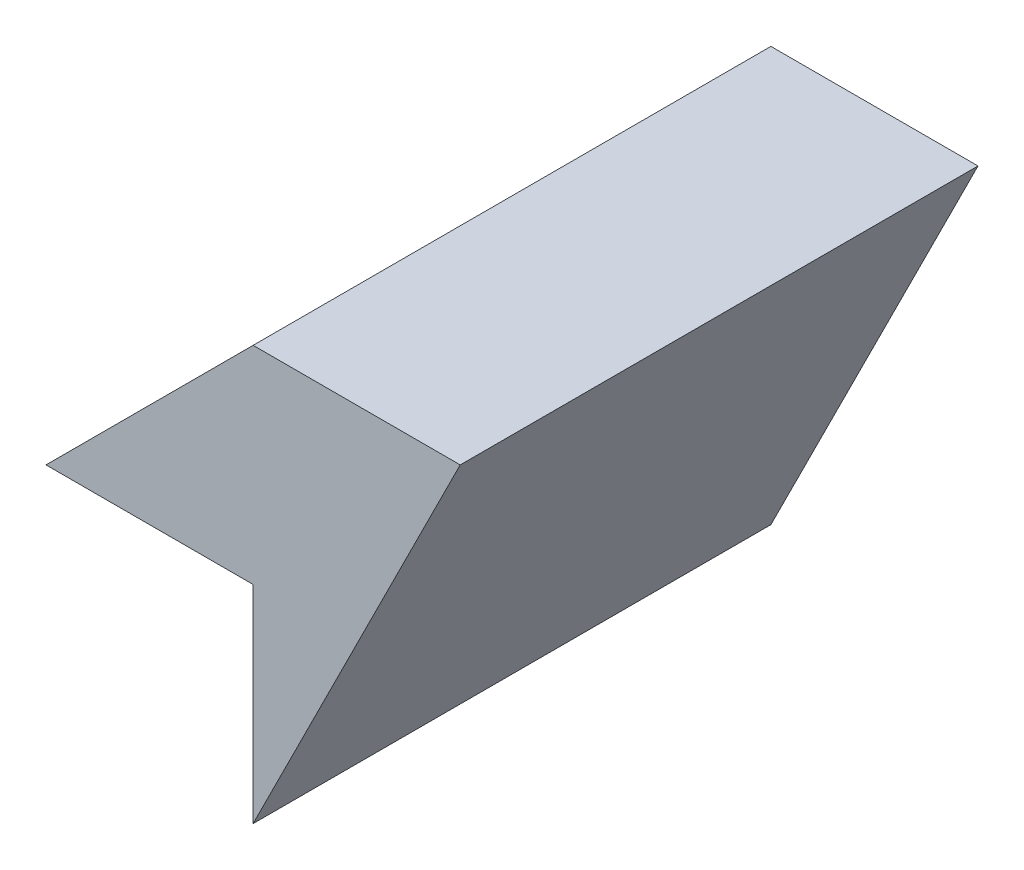
SolidWorks part; units mm, degrees
ref_plane "Front Plane" through (0, 0, 0) normal (0, 0, 1) x (1, 0, 0)
ref_plane "Top Plane" through (0, 0, 0) normal (0, 1, 0) x (1, 0, 0)
ref_plane "Right Plane" through (0, 0, 0) normal (1, 0, 0) x (0, 0, -1)
sketch "Sketch1" plane through (0, 0, 0) normal (0, 0, 1) x (1, 0, 0)
  line L0 (-20, -10) -> (-10, 0)
  line L1 (-10, 0) -> (0, 0)
  line L2 (0, 0) -> (-10, -20)
  line L3 (-10, -20) -> (-10, -10)
  line L4 (-10, -10) -> (-20, -10)
  dimension "D1" = 10
  dimension "D2" = 10
  dimension "D3" = 10
  dimension "D4" = 10
extrude "Boss-Extrude1" add sketch "Sketch1" along normal blind 25
